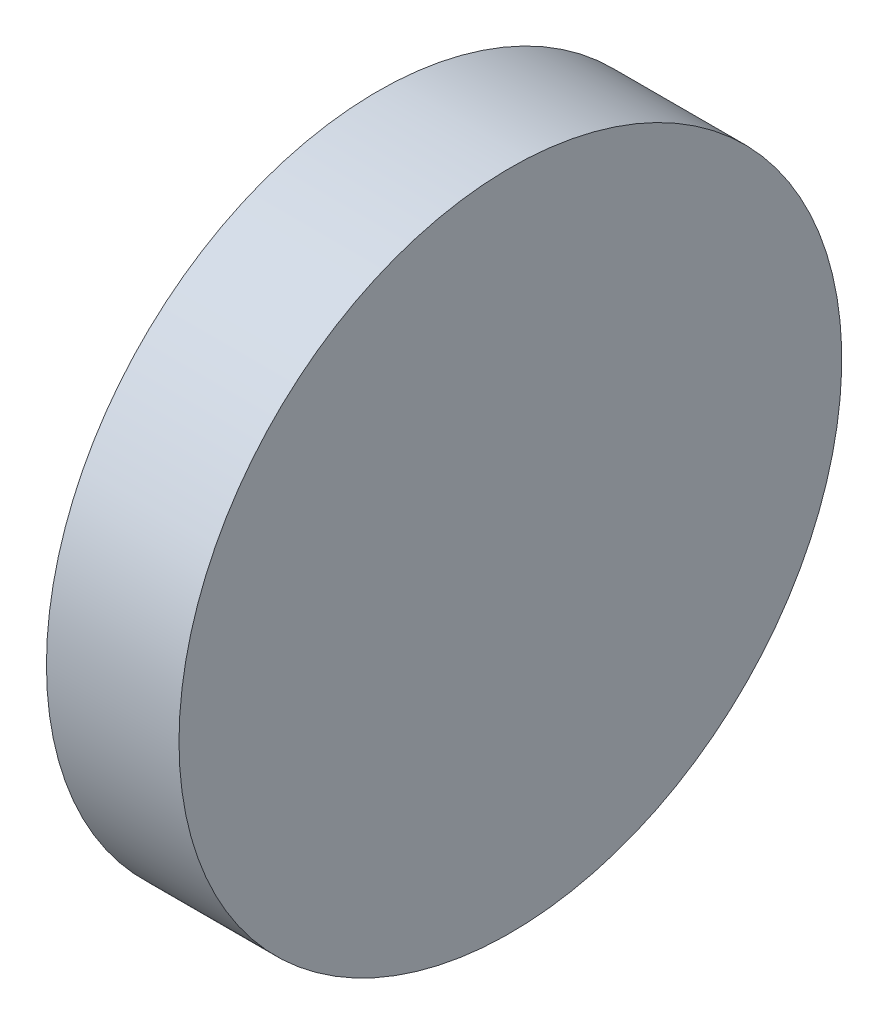
SolidWorks part; units mm, degrees
ref_plane "前视基准面" through (0, 0, 0) normal (0, 0, 1) x (1, 0, 0)
ref_plane "上视基准面" through (0, 0, 0) normal (0, 1, 0) x (1, 0, 0)
ref_plane "右视基准面" through (0, 0, 0) normal (1, 0, 0) x (0, 0, -1)
sketch "草图1" plane through (0, 0, 0) normal (0, 0, 1) x (1, 0, 0)
  line L0 (101.6003, 30.9173) -> (109.0603, 30.9173) construction
  line L1 (104.0629, 30.9173) -> (104.0629, 35.9173)
  line L2 (106.0629, 30.9173) -> (106.0629, 35.9173)
  line L3 (104.0629, 30.9173) -> (106.0629, 30.9173)
  line L5 (104.0629, 35.9173) -> (106.0629, 35.9173)
  dimension "D1" = 2
  dimension "D2" = 5
revolve "旋转1" add sketch "草图1" angle 360 about L0
